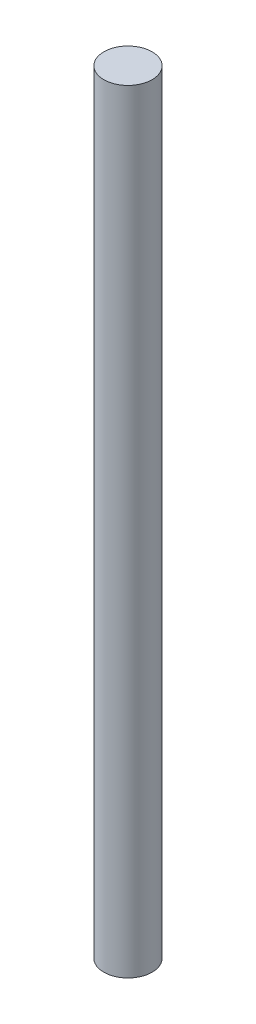
SolidWorks part; units mm, degrees
ref_plane "Front Plane" through (0, 0, 0) normal (0, 0, 1) x (1, 0, 0)
ref_plane "Top Plane" through (0, 0, 0) normal (0, 1, 0) x (1, 0, 0)
ref_plane "Right Plane" through (0, 0, 0) normal (1, 0, 0) x (0, 0, -1)
sketch "Sketch1" plane through (0, 0, 0) normal (0, 1, 0) x (1, 0, 0)
  circle A0 centre (0, 0) radius 3.9688
  dimension "D1" = 7.9375
extrude "Boss-Extrude1" add sketch "Sketch1" along normal blind 127
